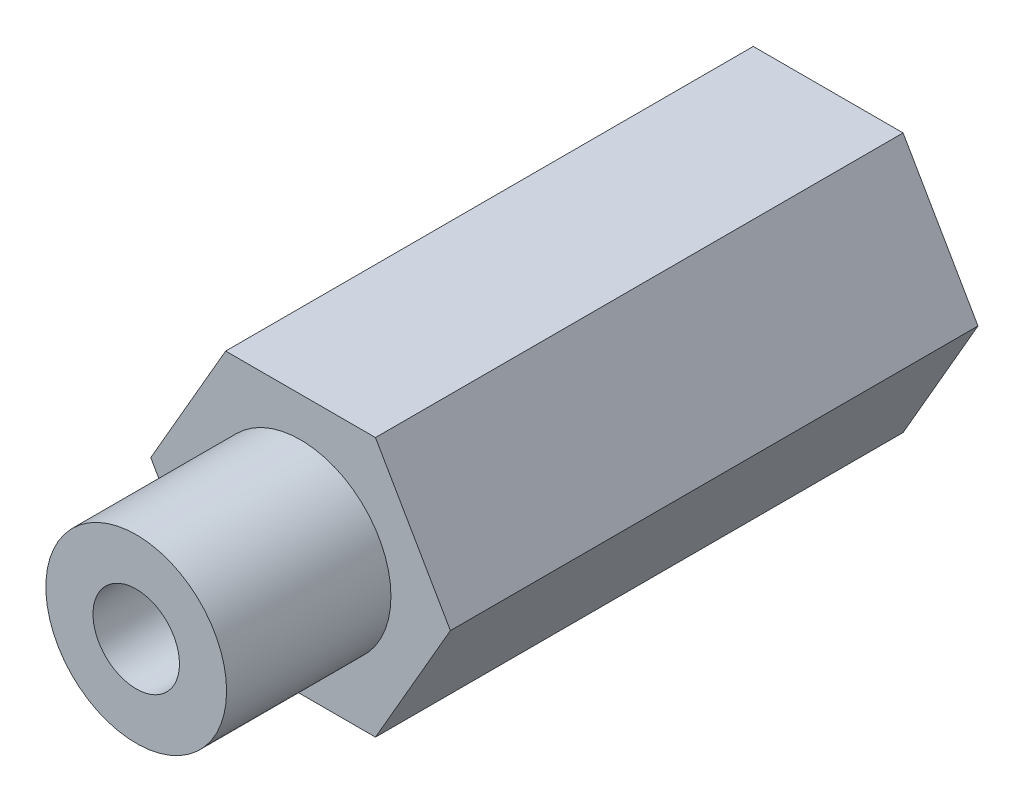
SolidWorks part; units mm, degrees
ref_plane "Front Plane" through (0, 0, 0) normal (1, 0, 0) x (0, 1, 0)
ref_plane "Top Plane" through (0, 0, 0) normal (0, 0, 1) x (0, 1, 0)
ref_plane "Right Plane" through (0, 0, 0) normal (0, 1, 0) x (-1, 0, 0)
sketch "Sketch1" plane through (0, 0, 0) normal (0, 0, 1) x (0, 1, 0)
  line L1 (9.525, -5.4993) -> (9.525, 5.4993)
  line L2 (9.525, 5.4993) -> (0, 10.9985)
  line L3 (0, 10.9985) -> (-9.525, 5.4993)
  line L4 (-9.525, 5.4993) -> (-9.525, -5.4993)
  line L5 (-9.525, -5.4993) -> (0, -10.9985)
  line L6 (0, -10.9985) -> (9.525, -5.4993)
  circle A0 centre (0, 0) radius 9.525 construction
  point P1 (0, 0)
  dimension "D1" = 19.05
extrude "Boss-Extrude1" add sketch "Sketch1" along normal blind 50.8
sketch "Sketch4" plane through (0, 0, 50.8) normal (0, 0, 1) x (1, 0, 0)
  circle A0 centre (0, 0) radius 3.175
  dimension "D1" = 6.35
extrude "Cut-Extrude2" cut sketch "Sketch4" against normal through all
sketch "Sketch2" plane through (0, 0, 50.8) normal (0, 0, 1) x (1, 0, 0)
  line L6 (10.9985, 0) -> (5.4993, 9.525)
  line L7 (5.4993, 9.525) -> (-5.4993, 9.525)
  line L8 (-5.4993, 9.525) -> (-10.9985, 0)
  line L9 (-10.9985, 0) -> (-5.4993, -9.525)
  line L10 (-5.4993, -9.525) -> (5.4993, -9.525)
  line L11 (5.4993, -9.525) -> (10.9985, 0)
  line L12 (10.9985, 0) -> (5.4993, 9.525)
  line L13 (5.4993, 9.525) -> (-5.4993, 9.525)
  line L14 (-5.4993, 9.525) -> (-10.9985, 0)
  line L15 (-10.9985, 0) -> (-5.4993, -9.525)
  line L16 (-5.4993, -9.525) -> (5.4993, -9.525)
  line L17 (5.4993, -9.525) -> (10.9985, 0)
  circle A0 centre (0, 0) radius 6.635
  dimension "D1" = 0
  dimension "D2" = 13.27
extrude "Cut-Extrude1" cut sketch "Sketch2" against normal blind 12.065
sketch "Sketch3" plane through (0, 0, 0) normal (0, 0, -1) x (1, 0, 0)
  circle A0 centre (0, 0) radius 6.86
  dimension "D1" = 13.72
extrude "Cut-Extrude3" cut sketch "Sketch3" against normal blind 12.065
sketch "Sketch5" plane through (-8.2489, -4.7625, 0) normal (-0.866, -0.5, 0) x (0.5, -0.866, 0)
  line L0 (-5.4993, 19.3675) -> (5.4993, 19.3675) construction
  line L4 (5.4993, 38.735) -> (-5.4993, 38.735)
  line L5 (-5.4993, 38.735) -> (-5.4993, 0)
  line L6 (-5.4993, 0) -> (5.4993, 0)
  line L7 (5.4993, 0) -> (5.4993, 38.735)
  line L8 (5.4993, 38.735) -> (-5.4993, 38.735) construction
  line L9 (-5.4993, 38.735) -> (-5.4993, 0) construction
  line L10 (-5.4993, 0) -> (5.4993, 0) construction
  line L11 (5.4993, 0) -> (5.4993, 38.735) construction
  circle A0 centre (0, 19.3675) radius 5.145
  point P2 (-5.4993, 19.3675)
  point P4 (5.4993, 19.3675)
  point P8 (0, 19.3675)
  dimension "D2" = 10.29
  dimension "D1" = 0
extrude "Cut-Extrude4" cut sketch "Sketch5" against normal blind 10
